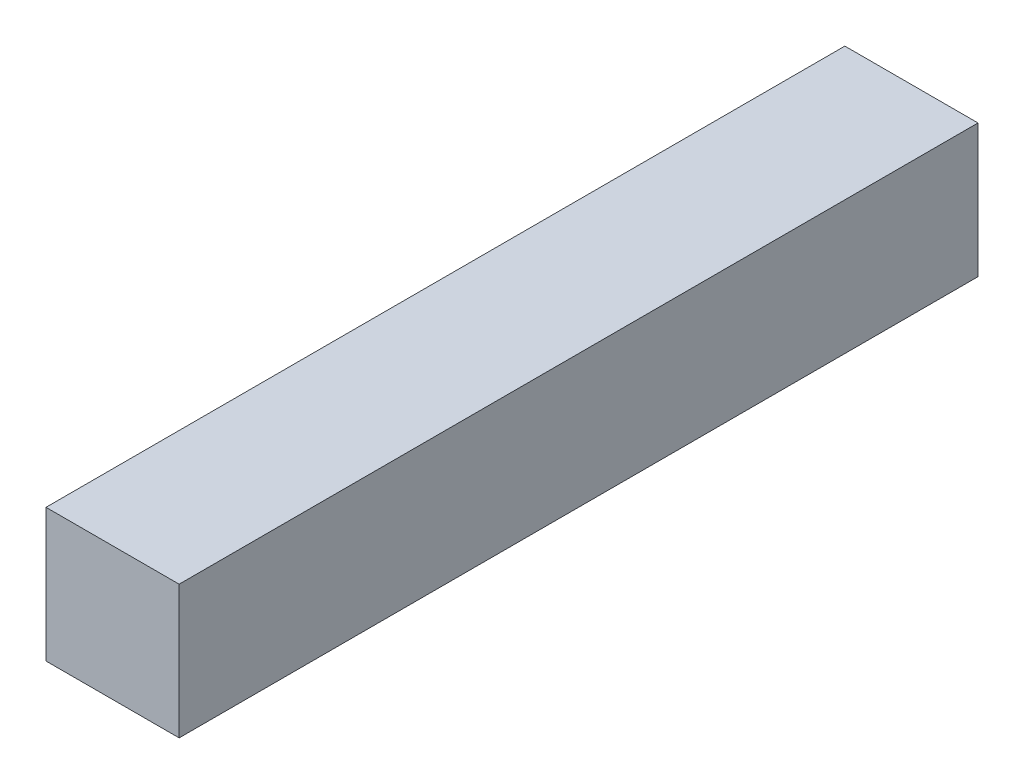
SolidWorks part; units mm, degrees
ref_plane "Front" through (0, 0, 0) normal (0, 0, 1) x (1, 0, 0)
ref_plane "Top" through (0, 0, 0) normal (0, 1, 0) x (1, 0, 0)
ref_plane "Right" through (0, 0, 0) normal (1, 0, 0) x (0, 0, -1)
sketch "Sketch1" plane through (0, 0, 0) normal (0, 0, 1) x (1, 0, 0)
  line L0 (0, 0) -> (15, 0)
  line L1 (0, 0) -> (0, 15)
  line L2 (15, 0) -> (15, 15)
  line L3 (0, 15) -> (15, 15)
  dimension "D1" = 15
  dimension "D2" = 15
extrude "Boss-Extrude1" add sketch "Sketch1" along normal blind 90
